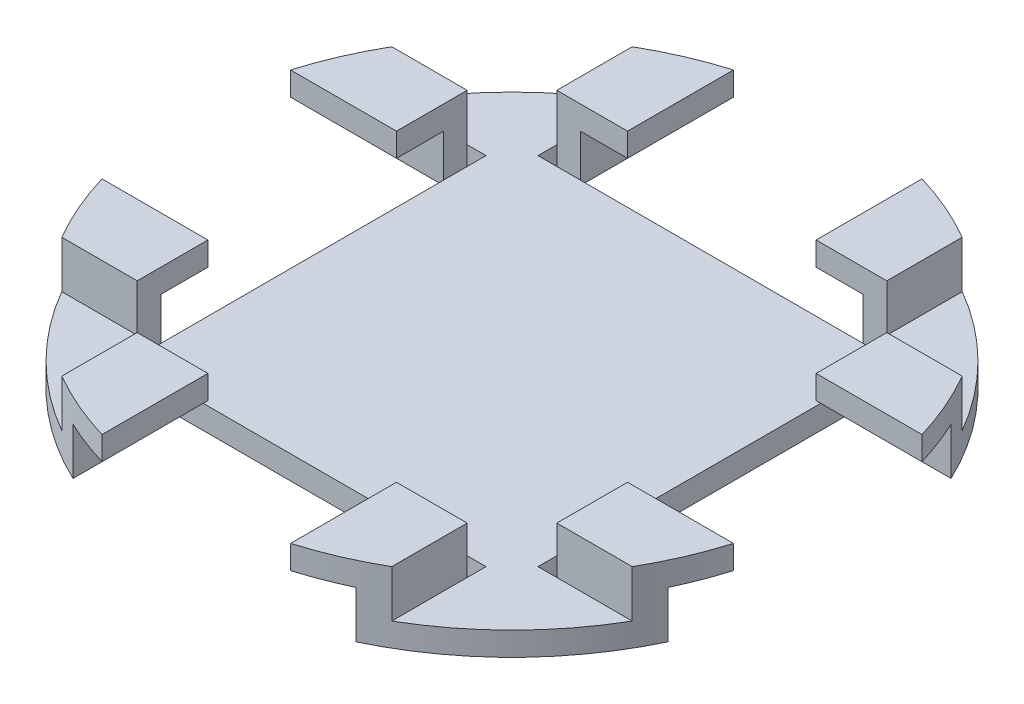
SolidWorks part; units mm, degrees
material "6061 Alloy"
ref_plane "Front Plane" through (0, 0, 0) normal (0, 0, 1) x (1, 0, 0)
ref_plane "Top Plane" through (0, 0, 0) normal (0, 1, 0) x (1, 0, 0)
ref_plane "Right Plane" through (0, 0, 0) normal (1, 0, 0) x (0, 0, -1)
sketch "Sketch1" plane through (0, 0, 0) normal (0, 1, 0) x (1, 0, 0)
  circle A0 centre (0, 0) radius 88.773
  dimension "D1" = 177.546
extrude "Base" add sketch "Sketch1" along normal blind 6.35
sketch "Sketch2" plane through (0, 6.35, 0) normal (0, 1, 0) x (1, 0, 0)
  line L3 (0, 0) -> (0, -88.773) construction
  line L4 (-44.45, -76.843) -> (-44.45, -51.443)
  line L5 (-44.45, -51.443) -> (0, -51.443)
  line L6 (0, -51.443) -> (44.45, -51.443)
  line L7 (44.45, -51.443) -> (44.45, -76.843)
  arc A1 (44.45, -76.843) -> (0, -88.773) centre (0, 0) cw
  arc A4 (-44.45, -76.843) -> (0, -88.773) centre (0, 0) ccw
  circle A6 centre (0, 0) radius 88.773 construction
  dimension "D1" = 44.45
  dimension "D2" = 25.4
extrude "Stopper" add sketch "Sketch2" along normal blind 12.7
sketch "Sketch5" plane through (0, 19.05, 0) normal (0, 1, 0) x (1, 0, 0)
  line L3 (0, 0) -> (0, -88.773) construction
  line L4 (-38.1, -80.1813) -> (-38.1, -51.443)
  line L5 (-38.1, -51.443) -> (0, -51.443)
  line L6 (0, -51.443) -> (38.1, -51.443)
  line L7 (38.1, -51.443) -> (38.1, -80.1813)
  line L13 (44.45, -51.443) -> (-44.45, -51.443) construction
  line L14 (-44.45, -51.443) -> (-44.45, -76.843) construction
  arc A1 (38.1, -80.1813) -> (0, -88.773) centre (0, 0) cw
  arc A4 (-38.1, -80.1813) -> (0, -88.773) centre (0, 0) ccw
  arc A7 (-44.45, -76.843) -> (44.45, -76.843) centre (0, 0) ccw construction
  dimension "D1" = 38.1
extrude "Stopper Gap" cut sketch "Sketch5" along direction (0, -1, 0) on the side against the normal through all from offset 6.35 offset against normal yes
sketch "Sketch6" plane through (0, 19.05, 0) normal (0, 1, 0) x (1, 0, 0)
  line L3 (0, 0) -> (0, -88.773) construction
  line L5 (-25.4, -51.443) -> (0, -51.443)
  line L6 (0, -51.443) -> (25.4, -51.443)
  line L10 (44.45, -51.443) -> (-44.45, -51.443) construction
  line L11 (-25.4, -85.0617) -> (-25.4, -56.523)
  line L12 (44.45, -76.843) -> (44.45, -51.443) construction
  line L13 (-44.45, -51.443) -> (-44.45, -76.843) construction
  line L14 (25.4, -85.0617) -> (25.4, -56.523)
  line L15 (-44.45, -51.443) -> (-25.4, -51.443)
  line L16 (-44.45, -51.443) -> (-44.45, -56.523)
  line L17 (-44.45, -56.523) -> (-25.4, -56.523)
  line L19 (25.4, -51.443) -> (44.45, -51.443)
  line L21 (25.4, -56.523) -> (44.45, -56.523)
  line L22 (44.45, -51.443) -> (44.45, -56.523)
  arc A1 (25.4, -85.0617) -> (0, -88.773) centre (0, 0) cw
  arc A4 (-25.4, -85.0617) -> (0, -88.773) centre (0, 0) ccw
  arc A5 (-44.45, -76.843) -> (44.45, -76.843) centre (0, 0) ccw construction
  dimension "D1" = 19.05
  dimension "D2" = 5.08
extrude "Overhang cut" cut sketch "Sketch6" against normal blind 26.416
pattern_circular "CirPattern1" count 4 over 360 about axis through (0, 0, 0) along (0, 1, 0) of "Overhang cut", "Stopper Gap", "Stopper"
